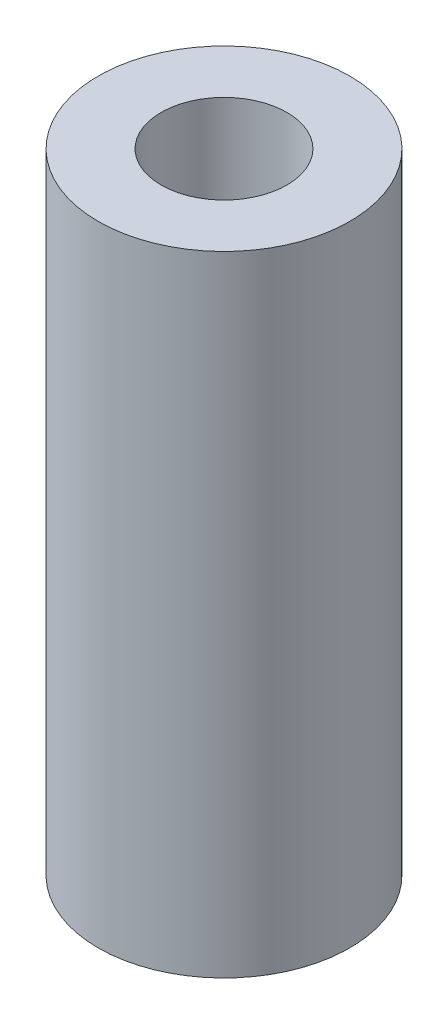
SolidWorks part; units mm, degrees
ref_plane "Front Plane" through (0, 0, 0) normal (0, 0, 1) x (1, 0, 0)
ref_plane "Top Plane" through (0, 0, 0) normal (0, 1, 0) x (1, 0, 0)
ref_plane "Right Plane" through (0, 0, 0) normal (1, 0, 0) x (0, 0, -1)
sketch "Sketch2" plane through (0, 0, 0) normal (0, 1, 0) x (1, 0, 0)
  circle A1 centre (0, 0) radius 2
extrude "Boss-Extrude1" add sketch "Sketch2" along normal blind 10
sketch "Sketch3" plane through (0, 10, 0) normal (0, 1, 0) x (1, 0, 0)
  circle A0 centre (0, 0) radius 1
extrude "Cut-Extrude1" cut sketch "Sketch3" against normal blind 10
